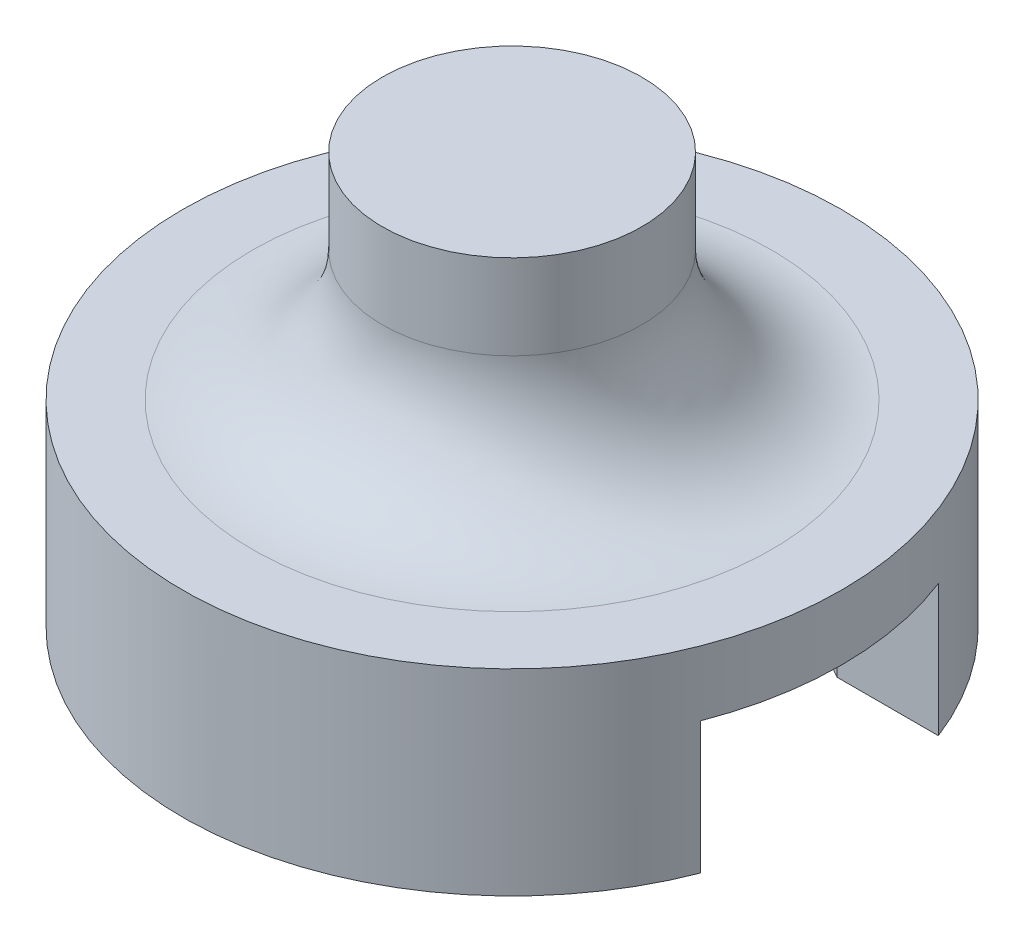
SolidWorks part; units mm, degrees
ref_plane "Front Plane" through (0, 0, 0) normal (0, 0, 1) x (1, 0, 0)
ref_plane "Top Plane" through (0, 0, 0) normal (0, 1, 0) x (1, 0, 0)
ref_plane "Right Plane" through (0, 0, 0) normal (1, 0, 0) x (0, 0, -1)
sketch "Sketch1" plane through (0, 0, 0) normal (0, 0, 1) x (1, 0, 0)
  line L0 (-10.1895, 0) -> (-10.1895, 9)
  line L1 (-10.1895, 9) -> (15.2105, 9)
  line L2 (15.2105, 9) -> (15.2105, 0)
  line L3 (15.2105, 0) -> (21.2105, 0)
  line L4 (21.2105, 0) -> (21.2105, 20.1735)
  line L5 (21.2105, 20.1735) -> (-16.1895, 20.1735)
  line L6 (-16.1895, 20.1735) -> (-16.1895, 0)
  line L7 (-16.1895, 0) -> (-10.1895, 0)
  dimension "D1" = 25.4
  dimension "D2" = 9
  dimension "D3" = 20.1735
  dimension "D4" = 6
  dimension "D5" = 6
extrude "Boss-Extrude1" add sketch "Sketch1" along normal blind 25.4
sketch "Sketch3" plane through (0, 20.1735, 0) normal (0, 1, 0) x (1, 0, 0)
  line L0 (21.2105, -12.7) -> (-16.1895, -12.7) construction
  line L1 (21.2105, -25.4) -> (21.2105, 0) construction
  line L13 (-16.1895, -25.4) -> (-16.1895, 0) construction
  line L14 (21.2105, 0) -> (-16.1895, 0) construction
  line L15 (-16.1895, -12.7) -> (21.2105, -12.7) construction
  line L17 (10.448, -17.2827) -> (10.448, -8.1173)
  line L18 (10.448, -8.1173) -> (2.5105, -3.5346)
  line L19 (2.5105, -3.5346) -> (-5.427, -8.1173)
  line L20 (-5.427, -8.1173) -> (-5.427, -17.2827)
  line L21 (-5.427, -17.2827) -> (2.5105, -21.8654)
  line L22 (2.5105, -21.8654) -> (10.448, -17.2827)
  line L23 (21.2105, -8.1173) -> (10.448, -8.1173)
  line L24 (21.2105, -8.1173) -> (21.2105, -17.2827)
  line L25 (21.2105, -17.2827) -> (10.448, -17.2827)
  line L26 (10.448, -8.1173) -> (10.448, -17.2827)
  circle A2 centre (2.5105, -12.7) radius 7.9375 construction
  circle A3 centre (2.5105, -12.7) radius 12.7
  dimension "D1" = 15.875
extrude "Boss-Extrude3" add sketch "Sketch3" along normal blind 5.08 contours A3 L25 L22 L21 L20 L19 L18 L23
sketch "Sketch4" plane through (0, 20.1735, 0) normal (0, 1, 0) x (1, 0, 0)
  line L1 (21.2105, 0) -> (-16.1895, 0)
  line L2 (21.2105, 0) -> (21.2105, -25.4)
  line L3 (21.2105, -25.4) -> (-16.1895, -25.4)
  line L4 (-16.1895, 0) -> (-16.1895, -25.4)
extrude "Cut-Extrude1" cut sketch "Sketch4" against normal blind 25.4
sketch "Sketch5" plane through (0, 25.2535, 0) normal (0, 1, 0) x (1, 0, 0)
  line L7 (14.3548, -17.2827) -> (10.448, -17.2827)
  line L8 (10.448, -17.2827) -> (2.5105, -21.8654)
  line L9 (2.5105, -21.8654) -> (-5.427, -17.2827)
  line L10 (-5.427, -17.2827) -> (-5.427, -8.1173)
  line L11 (-5.427, -8.1173) -> (2.5105, -3.5346)
  line L12 (2.5105, -3.5346) -> (10.448, -8.1173)
  line L13 (10.448, -8.1173) -> (14.3548, -8.1173)
  line L14 (14.3548, -17.2827) -> (10.448, -17.2827)
  line L15 (10.448, -17.2827) -> (2.5105, -21.8654)
  line L16 (2.5105, -21.8654) -> (-5.427, -17.2827)
  line L17 (-5.427, -17.2827) -> (-5.427, -8.1173)
  line L18 (-5.427, -8.1173) -> (2.5105, -3.5346)
  line L19 (2.5105, -3.5346) -> (10.448, -8.1173)
  line L20 (10.448, -8.1173) -> (14.3548, -8.1173)
  circle A1 centre (2.5105, -12.7) radius 12.7
  arc A2 (14.3548, -8.1173) -> (14.3548, -17.2827) centre (2.5105, -12.7) ccw
  arc A3 (14.3548, -8.1173) -> (14.3548, -17.2827) centre (2.5105, -12.7) ccw
  dimension "D1" = 0
extrude "Boss-Extrude4" add sketch "Sketch5" along normal blind 2.5 contours A1
sketch "Sketch6" plane through (0, 27.7535, 0) normal (0, 1, 0) x (1, 0, 0)
  circle A1 centre (2.5105, -12.7) radius 5
  circle A2 centre (2.5105, -12.7) radius 12.7
  circle A3 centre (2.5105, -12.7) radius 12.7
  dimension "D1" = 0
  dimension "D2" = 10
extrude "Boss-Extrude5" add sketch "Sketch6" along normal blind 8.272 contours A1
fillet "Fillet1" radius 5 1 edges at (-2.4895, 27.7535, 12.7)
